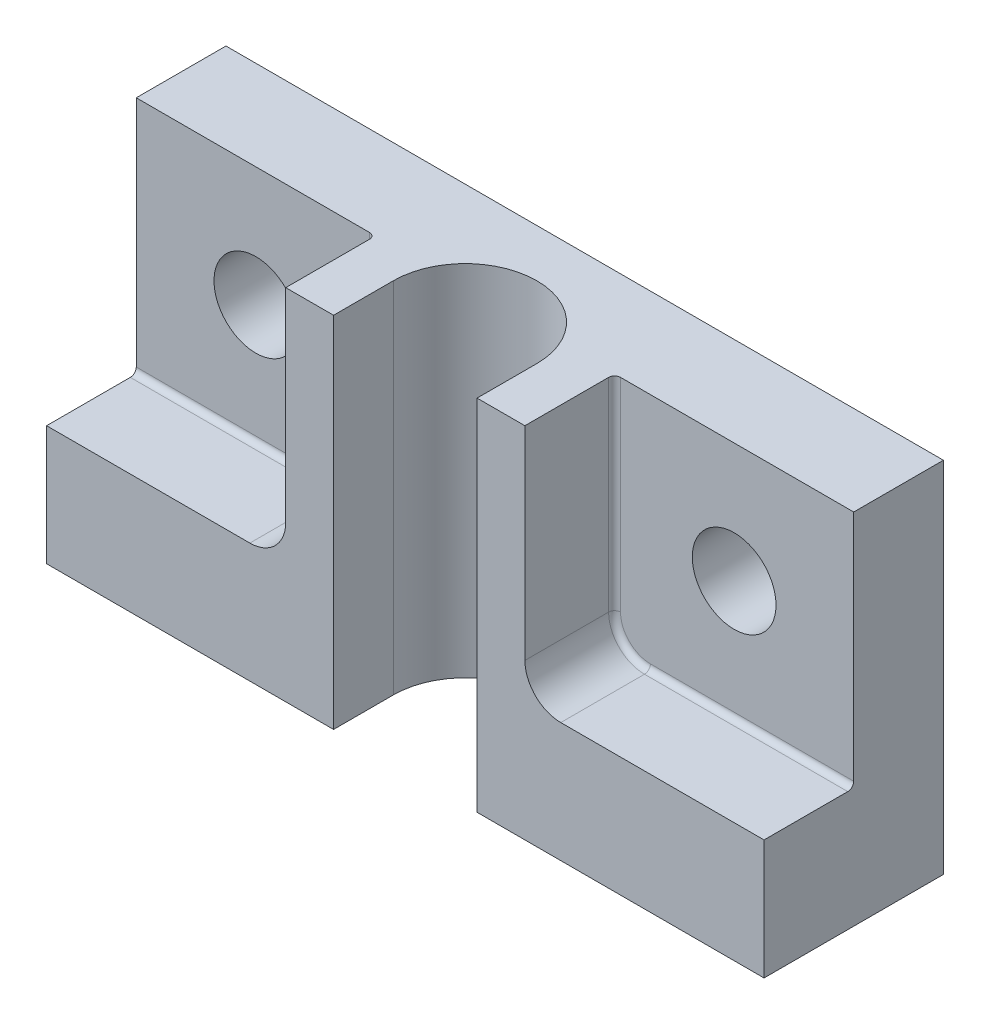
SolidWorks part; units mm, degrees
ref_plane "Front Plane" through (0, 0, 0) normal (0, 0, 1) x (1, 0, 0)
ref_plane "Top Plane" through (0, 0, 0) normal (0, 1, 0) x (1, 0, 0)
ref_plane "Right Plane" through (0, 0, 0) normal (1, 0, 0) x (0, 0, -1)
other "Configuration Table"
sketch "Sketch1" plane through (0, 0, 0) normal (0, 0, 1) x (1, 0, 0)
  line L1 (-30, 0) -> (30, 0)
  line L2 (-30, 0) -> (-30, -30)
  line L3 (-30, -30) -> (30, -30)
  line L4 (30, 0) -> (30, -30)
  circle A0 centre (20, -10) radius 3.5
  circle A1 centre (-20, -10) radius 3.5
  dimension "D1" = 60
  dimension "D2" = 30
extrude "Extrude1" add sketch "Sketch1" against normal blind 15
sketch "Sketch2" plane through (0, 0, 0) normal (0, 0, 1) x (1, 0, 0)
  line L0 (30, -30) -> (30, 0) construction
  line L1 (13, -20) -> (30, -20)
  line L2 (10, -17) -> (10, 0)
  line L3 (10, 0) -> (30, 0)
  line L4 (30, -20) -> (30, 0)
  line L5 (30, 0) -> (-30, 0) construction
  line L6 (0, 10) -> (0, -40) construction
  line L7 (-30, -20) -> (-30, 0)
  line L8 (-10, 0) -> (-30, 0)
  line L9 (-10, -17) -> (-10, 0)
  line L10 (-13, -20) -> (-30, -20)
  arc A0 (13, -20) -> (10, -17) centre (13, -17) cw
  arc A1 (-13, -20) -> (-10, -17) centre (-13, -17) ccw
  dimension "D1" = 3
  dimension "D2" = 20
extrude "Extrude2" cut sketch "Sketch2" against normal blind 7.5
sketch "Sketch3" plane through (0, 0, 0) normal (0, 1, 0) x (1, 0, 0)
  line L1 (0, 0) -> (0, 5) construction
  line L2 (6, 0) -> (6, 5)
  line L3 (-6, 0) -> (-6, 5)
  line L4 (-6, 0) -> (6, 0)
  arc A1 (6, 5) -> (-6, 5) centre (0, 5) ccw
  dimension "D1" = 5
  dimension "D2" = 6
  dimension "D3" = 6
extrude "Extrude3" cut sketch "Sketch3" against normal through all
fillet "Fillet1" radius 0.5 6 edges at (-10, -8.5, -7.5) (-10.8787, -19.1213, -7.5) (10, -8.5, -7.5) (10.8787, -19.1213, -7.5) (-21.5, -20, -7.5) (21.5, -20, -7.5)
